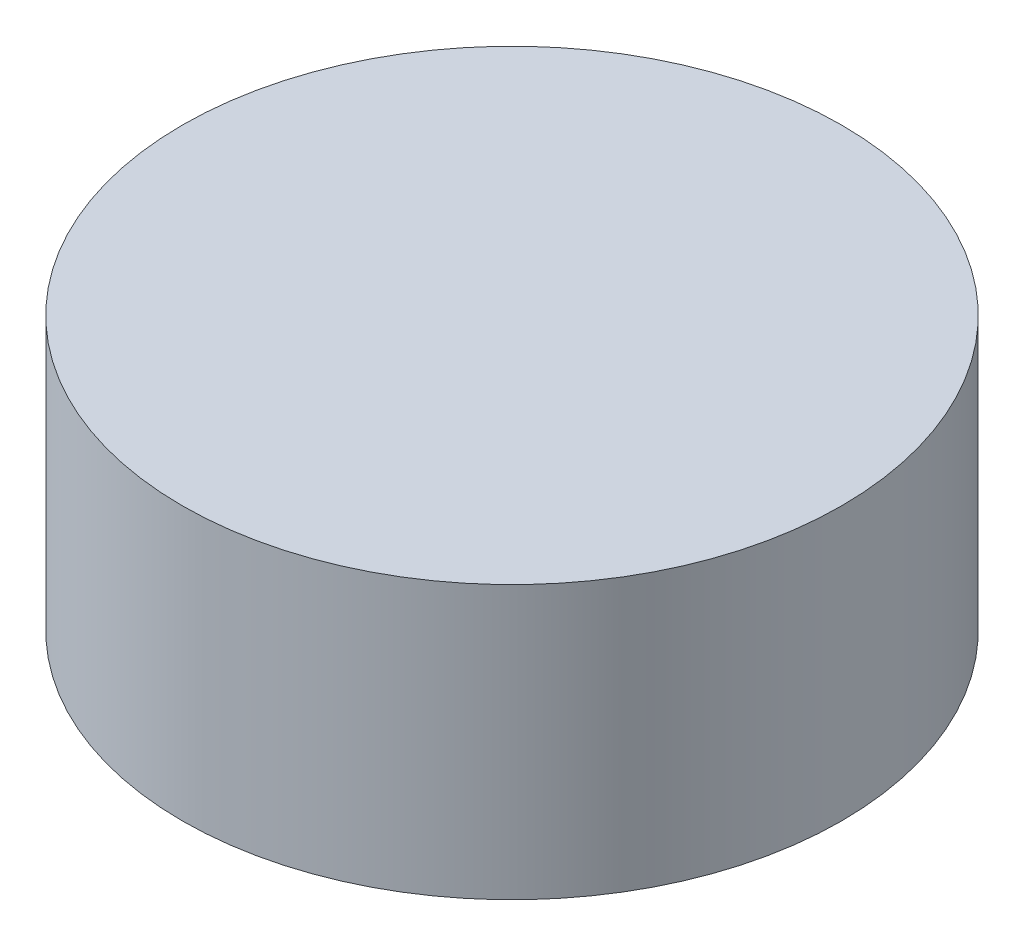
SolidWorks part; units mm, degrees
ref_plane "Front Plane" through (0, 0, 0) normal (0, 0, 1) x (1, 0, 0)
ref_plane "Top Plane" through (0, 0, 0) normal (0, 1, 0) x (1, 0, 0)
ref_plane "Right Plane" through (0, 0, 0) normal (1, 0, 0) x (0, 0, -1)
sketch "Sketch1" plane through (0, 0, 0) normal (0, 1, 0) x (1, 0, 0)
  line L0 (0, 0) -> (0, 15.15) construction
  line L1 (0, 15.15) -> (-100.9, 15.15) construction
  line L2 (-100.9, 15.15) -> (-100.9, -15.15) construction
  line L3 (-100.9, -15.15) -> (10.4, -15.15) construction
  line L4 (10.4, -15.15) -> (10.4, 15.15) construction
  line L5 (10.4, 15.15) -> (0, 15.15) construction
  line L6 (0, 0) -> (10.4, 0) construction
  line L7 (0, 0) -> (-100.9, 0) construction
  line L8 (-3.6, 0) -> (-3.6, 20) construction
  line L9 (10.4, 0) -> (19.6, 0) construction
  line L10 (-59.2, 0) -> (-59.2, 24.5) construction
  line L11 (-64.1, 0) -> (-64.1, 15.15) construction
  line L12 (-64.1, 0) -> (-64.1, -5.1) construction
  line L13 (-64.1, -5.1) -> (-109.1, -5.1) construction
  line L14 (-24.8, 0) -> (-24.8, 17.7) construction
  dimension "D1" = 30.3
  dimension "D2" = 111.3
  dimension "D3" = 10.4
  dimension "D4" = 3.6
  dimension "D5" = 20
  dimension "D6" = 19.6
  dimension "D7" = 24.8
  dimension "D8" = 5.1
  dimension "D9" = 45
  dimension "D10" = 64.1
  dimension "D11" = 24.5
  dimension "D12" = 59.2
  dimension "D13" = 17.7
sketch "Sketch3" plane through (0, 0, 0) normal (0, 1, 0) x (1, 0, 0)
  line L0 (0, 0) -> (0, -19.3) construction
  line L1 (-27.1, 0) -> (-27.1, -17.4) construction
  line L2 (0, 0) -> (-100.9, 0) construction
  line L3 (-72, 0) -> (-72, -28.6) construction
  dimension "D1" = 19.3
  dimension "D2" = 17.4
  dimension "D3" = 28.6
  dimension "D4" = 27.1
  dimension "D5" = 72
sketch "Sketch2" plane through (0, 0, 0) normal (0, 1, 0) x (1, 0, 0)
  line L0 (19.6, -11.1333) -> (19.6, 11.1333) construction
  line L1 (-82.9362, -28.6) -> (-59.2746, -28.6) construction
  line L3 (-38.3758, -17.4) -> (-20.5335, -17.4) construction
  line L4 (-6.8012, -19.3) -> (7.7138, -19.3) construction
  line L5 (-44.6362, 24.5) -> (-71.0994, 24.5) construction
  line L6 (-20.2625, 17.7) -> (-32.3488, 17.7) construction
  line L7 (5.0808, 20) -> (-8.6275, 20) construction
  line L8 (19.6, -12.7653) -> (19.6, 13.2246) construction
  spline S0 degree 3 poles (-109.1, -5.1) (-109.4246, 10.4415) (-73.7876, 25.2227) (-43.0203, 23.9373) (-34.2195, 17.8508) (-19.7454, 17.5568) (-9.8315, 20.0896) (7.1736, 19.9352) (19.6, 14.2893) (19.6, 0) knots 0 0 0 0 0.230584 0.286176 0.525951 0.574149 0.719962 0.76437 1 1 1 1
  spline S1 degree 3 poles (19.6, 0) (19.6, -12.7982) (9.6283, -19.5586) (-8.5374, -19.1352) (-19.7964, -17.3572) (-41.2186, -17.3729) (-58.114, -28.9795) (-85.1554, -28.3277) (-109.1, -26.6433) (-109.1, -5.1) knots 0 0 0 0 0.17462 0.213185 0.36648 0.418282 0.679408 0.740843 1 1 1 1
  point P0 (-59.2, 24.5)
  point P2 (-3.6, 20)
  point P4 (19.6, 0)
  point P6 (-109.1, -5.1)
  point P8 (-24.8, 17.7)
extrude "Boss-Extrude1" add sketch "Sketch2" along normal blind 10
sketch "Sketch4" plane through (0, 10, 0) normal (0, 1, 0) x (1, 0, 0)
  line L0 (32.8419, 36.6353) -> (-119.9171, 36.6353)
  line L2 (32.8419, 36.6353) -> (32.8419, -33.3882)
  line L5 (-119.9171, 36.6353) -> (-119.9171, -33.3882)
  line L6 (-119.9171, -33.3882) -> (32.8419, -33.3882)
  circle A0 centre (-46.4462, 0) radius 12.08
extrude "Cut-Extrude1" cut sketch "Sketch4" against normal through all
